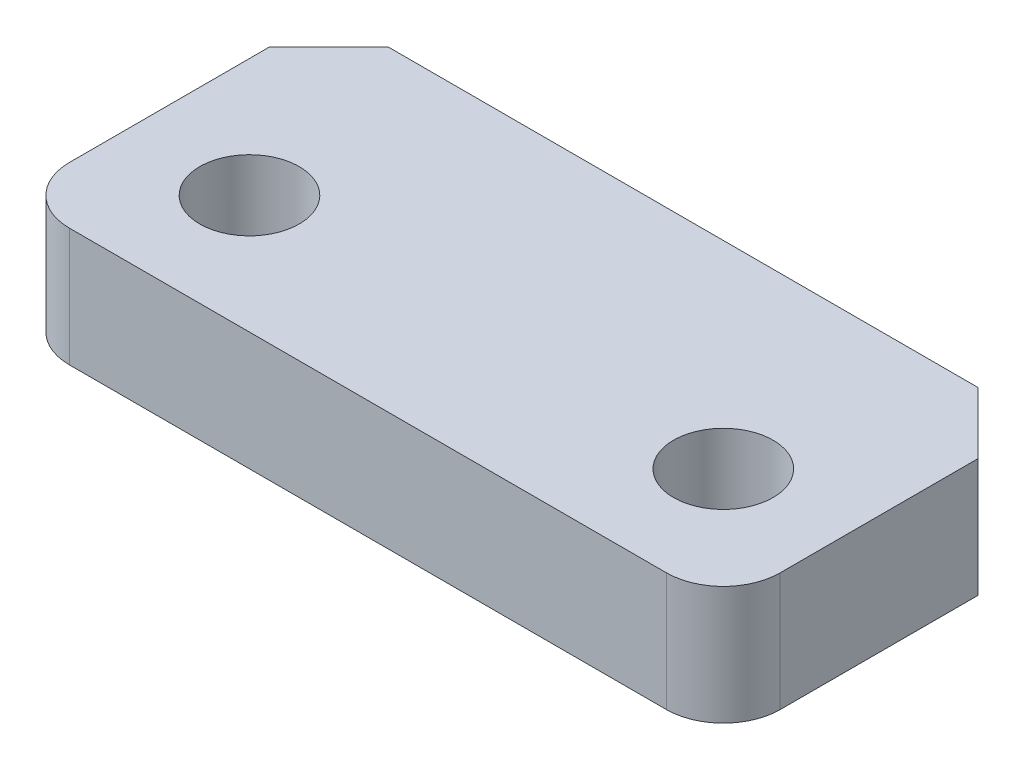
SolidWorks part; units mm, degrees
ref_plane "Front Plane" through (0, 0, 0) normal (0, 0, 1) x (1, 0, 0)
ref_plane "Top Plane" through (0, 0, 0) normal (0, 1, 0) x (1, 0, 0)
ref_plane "Right Plane" through (0, 0, 0) normal (1, 0, 0) x (0, 0, -1)
sketch "Sketch1" plane through (0, 0, 0) normal (0, 1, 0) x (1, 0, 0)
  line L1 (-19.05, -10.6045) -> (19.05, -10.6045)
  line L2 (-19.05, -10.6045) -> (-19.05, 10.6045)
  line L3 (-19.05, 10.6045) -> (19.05, 10.6045)
  line L4 (19.05, -10.6045) -> (19.05, 10.6045)
  line L5 (-19.05, -10.6045) -> (19.05, 10.6045) construction
  line L6 (-19.05, 10.6045) -> (19.05, -10.6045) construction
  point P0 (0, 0)
extrude "Boss-Extrude1" add sketch "Sketch1" along normal blind 6.35
sketch "Sketch2" plane through (0, 6.35, 0) normal (0, 1, 0) x (1, 0, 0)
  line L3 (0, 0) -> (-12.7, 0)
  line L4 (0, 0) -> (12.7, 0)
  circle A0 centre (-12.7, 0) radius 2.667
  circle A3 centre (12.7, 0) radius 2.667
  dimension "D1" = 12.7
  dimension "D2" = 12.7
extrude "Cut-Extrude1" cut sketch "Sketch2" against normal blind 9.525
sketch "Sketch3" plane through (0, 6.35, 0) normal (0, 1, 0) x (1, 0, 0)
  line L0 (-19.05, 10.6045) -> (-15.875, 10.6045)
  line L1 (19.05, 10.6045) -> (-19.05, 10.6045) construction
  line L2 (-15.875, 10.6045) -> (-19.05, 7.4295)
  line L3 (-19.05, 10.6045) -> (-19.05, -10.6045) construction
  line L4 (-19.05, 7.4295) -> (-19.05, 10.6045)
  line L5 (19.05, 10.6045) -> (15.748, 10.6045)
  line L6 (15.748, 10.6045) -> (19.05, 7.3025)
  line L7 (19.05, -10.6045) -> (19.05, 10.6045) construction
  line L8 (19.05, 7.3025) -> (19.05, 10.6045)
  line L9 (19.05, -10.6045) -> (15.748, -10.6045)
  line L10 (-19.05, -10.6045) -> (19.05, -10.6045) construction
  line L11 (15.748, -10.6045) -> (19.05, -7.3025)
  line L12 (19.05, -7.3025) -> (19.05, -10.6045)
  line L13 (-19.05, -10.6045) -> (-15.875, -10.6045)
  line L14 (-15.875, -10.6045) -> (-19.05, -7.4295)
  line L15 (-19.05, -7.4295) -> (-19.05, -10.6045)
  dimension "D1" = 3.175
  dimension "D2" = 3.302
extrude "Cut-Extrude2" cut sketch "Sketch3" against normal blind 9.525
sketch "Sketch4" plane through (0, 6.35, 0) normal (0, 1, 0) x (1, 0, 0)
  line L1 (19.05, -7.3025) -> (15.748, -10.6045)
  line L2 (15.748, -10.6045) -> (-15.875, -10.6045)
  line L3 (-15.875, -10.6045) -> (-19.05, -7.4295)
  line L4 (-15.875, -10.6045) -> (-15.875, -6.35)
  line L5 (-15.875, -6.35) -> (-19.05, -6.35)
  line L6 (-19.05, 7.4295) -> (-19.05, -7.4295) construction
  line L7 (-19.05, -6.35) -> (-19.05, -7.4295)
  line L8 (-15.875, -6.35) -> (19.05, -6.35)
  line L9 (19.05, -7.3025) -> (19.05, 7.3025) construction
  line L10 (19.05, -6.35) -> (19.05, -7.3025)
  line M7 (-19.05, 7.4295) -> (-19.05, -7.4295)
  line M8 (-19.05, -7.4295) -> (-15.875, -10.6045)
  line M9 (-15.875, -10.6045) -> (15.748, -10.6045)
  line M10 (15.748, -10.6045) -> (19.05, -7.3025)
  line M11 (19.05, -7.3025) -> (19.05, 7.3025)
  dimension "D1" = 4.2545
extrude "Cut-Extrude4" cut sketch "Sketch4" against normal blind 9.525 contours L4 L5 M7 M8 | L8 L4 M9 M10 M11
fillet "Fillet2" radius 3.048 2 edges at (19.05, 3.175, 6.35) (-19.05, 3.175, 6.35)
